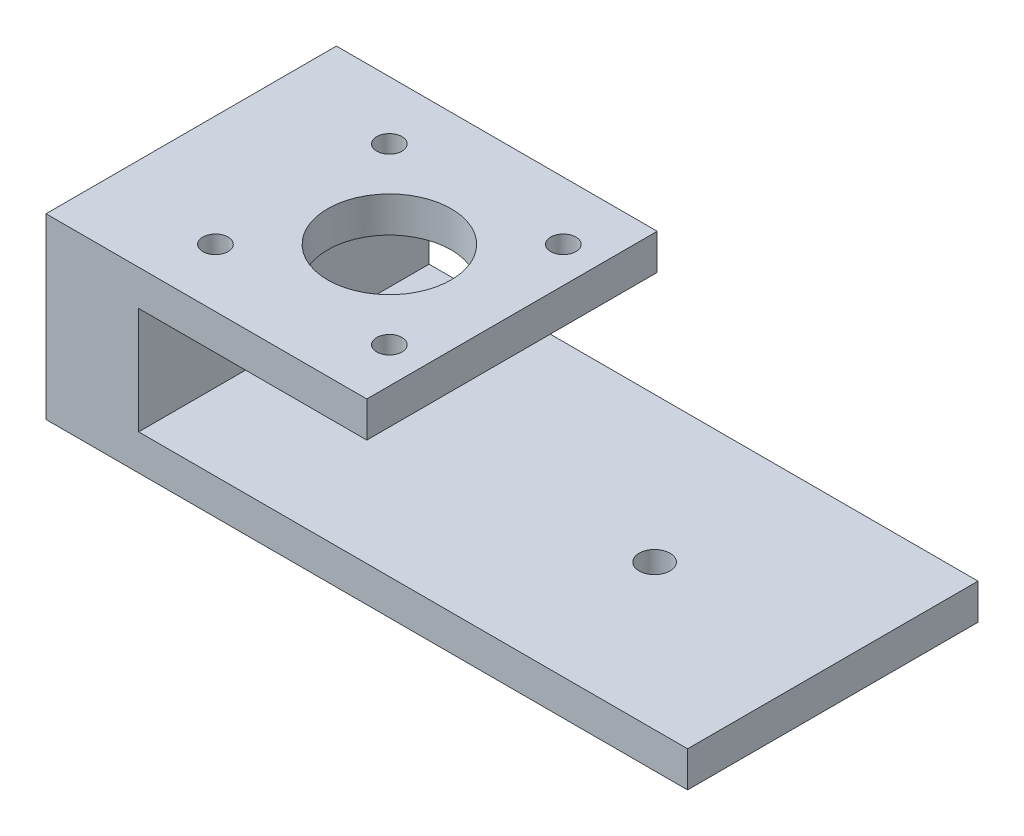
SolidWorks part; units mm, degrees
ref_plane "Front Plane" through (0, 0, 0) normal (0, 0, 1) x (1, 0, 0)
ref_plane "Top Plane" through (0, 0, 0) normal (0, 1, 0) x (1, 0, 0)
ref_plane "Right Plane" through (0, 0, 0) normal (1, 0, 0) x (0, 0, -1)
sketch "Sketch1" plane through (0, 0, 0) normal (0, 1, 0) x (1, 0, 0)
  line L1 (57.15, 25.8699) -> (-57.15, 25.8699)
  line L2 (57.15, 25.8699) -> (57.15, -25.8699)
  line L3 (57.15, -25.8699) -> (-57.15, -25.8699)
  line L4 (-57.15, 25.8699) -> (-57.15, -25.8699)
  point P4 (-57.15, 0)
  point P6 (0, 25.8699)
  dimension "D1" = 51.7398
  dimension "D2" = 114.3
extrude "Boss-Extrude1" add sketch "Sketch1" along normal blind 6.35
hole_wizard "M5 Clearance Hole1" positions "Sketch2" profile "Sketch4" hole size "M5" standard "ANSI Metric" end condition up to next
sketch "Sketch2" plane through (0, 6.35, 0) normal (0, 1, 0) x (1, 0, 0)
  line L1 (-21.844, 0) -> (25.4, 0) construction
  line L3 (57.15, -25.8699) -> (57.15, 25.8699) construction
  line L4 (0, 25.8699) -> (0, -25.8699) construction
  line L5 (57.15, 25.8699) -> (-57.15, 25.8699) construction
  line L6 (-57.15, -25.8699) -> (57.15, -25.8699) construction
  point P0 (25.4, 0)
  point P2 (-21.844, 0)
  dimension "D1" = 47.244
  dimension "D2" = 31.75
sketch "Sketch4" plane through (25.4, 6.35, 0) normal (1, 0, 0) x (0, 0, 1)
  line L0 (0, 0) -> (0, 6.35)
  line L1 (0, 6.35) -> (2.75, 6.35)
  line L2 (2.75, 6.35) -> (2.75, 0)
  line L5 (2.75, 0) -> (0, 0)
  line L11 (0, -6.35) -> (0, 107.95) construction
  dimension "Thru Hole Dia." = 5.5
  dimension "Thru Hole Depth" = 6.35
sketch "Sketch6" plane through (0, 6.35, 0) normal (0, 1, 0) x (1, 0, 0)
  line L0 (-57.15, -25.8699) -> (57.15, -25.8699) construction
  line L1 (-57.15, 25.8699) -> (-40.64, 25.8699)
  line L2 (-57.15, 25.8699) -> (-57.15, -25.8699)
  line L3 (-57.15, -25.8699) -> (-40.64, -25.8699)
  line L4 (-40.64, 25.8699) -> (-40.64, -25.8699)
  dimension "D1" = 16.51
extrude "Boss-Extrude2" add sketch "Sketch6" along normal blind 19.05
sketch "Sketch7" plane through (0, 25.4, 0) normal (0, 1, 0) x (1, 0, 0)
  line L1 (-57.15, -25.8699) -> (0, -25.8699)
  line L2 (-57.15, -25.8699) -> (-57.15, 25.8699)
  line L3 (-57.15, 25.8699) -> (0, 25.8699)
  line L4 (0, -25.8699) -> (0, 25.8699)
  dimension "D1" = 57.15
extrude "Boss-Extrude3" add sketch "Sketch7" along normal blind 6.35
sketch "Sketch10" plane through (0, 31.75, 0) normal (0, 1, 0) x (1, 0, 0)
  line L0 (-21.844, 0) -> (71.0771, 0) construction
  circle A0 centre (-21.844, 0) radius 10.9982
  circle A1 centre (-21.844, 0) radius 2.75 construction
  dimension "D1" = 21.9964
extrude "Cut-Extrude1" cut sketch "Sketch10" against normal up to surface (6.35 mm away) up to face at (-20.32, 25.4, 0)
hole_wizard "M4 Clearance Hole1" positions "Sketch11" profile "Sketch12" hole size "M4" standard "ANSI Metric" end condition up to next
sketch "Sketch11" plane through (0, 31.75, 0) normal (0, 1, 0) x (1, 0, 0)
  line L0 (-37.338, -15.494) -> (-6.35, -15.494) construction
  line L2 (-37.338, 15.494) -> (-37.338, -15.494) construction
  line L3 (-37.338, 15.494) -> (-6.35, -15.494) construction
  circle A0 centre (-21.844, 0) radius 10.9982 construction
  point P0 (-6.35, 15.494)
  point P2 (-37.338, 15.494)
  point P4 (-37.338, -15.494)
  point P6 (-6.35, -15.494)
  point P22 (-37.338, 0)
  point P53 (-21.844, 0)
  dimension "D1" = 30.988
  dimension "D2" = 30.988
sketch "Sketch12" plane through (-6.35, 31.75, -15.494) normal (1, 0, 0) x (0, 0, 1)
  line L0 (0, 0) -> (0, 6.35)
  line L1 (0, 6.35) -> (2.25, 6.35)
  line L2 (2.25, 6.35) -> (2.25, 0)
  line L5 (2.25, 0) -> (0, 0)
  line L11 (0, -6.35) -> (0, 107.95) construction
  dimension "Thru Hole Dia." = 4.5
  dimension "Thru Hole Depth" = 6.35
